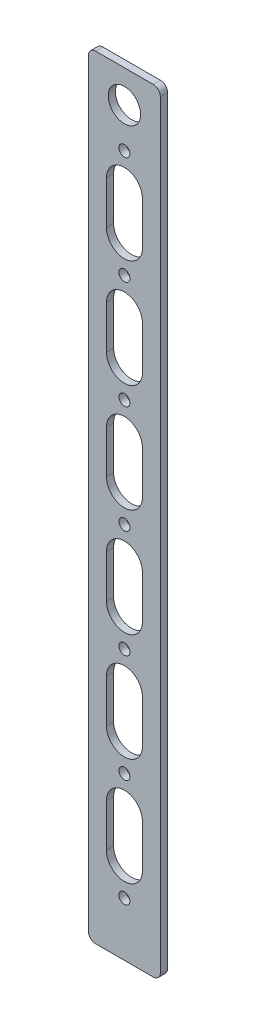
SolidWorks part; units mm, degrees
material "环氧玻璃布层压板"
ref_plane "前视基准面" through (0, 0, 0) normal (0, 0, 1) x (1, 0, 0)
ref_plane "上视基准面" through (0, 0, 0) normal (0, 1, 0) x (1, 0, 0)
ref_plane "右视基准面" through (0, 0, 0) normal (1, 0, 0) x (0, 0, -1)
sketch "草图1" plane through (0, 0, 0) normal (0, 0, 1) x (1, 0, 0)
  line L1 (-10, -107.5) -> (10, -107.5)
  line L2 (-10, -107.5) -> (-10, 107.5)
  line L3 (-10, 107.5) -> (10, 107.5)
  line L4 (10, -107.5) -> (10, 107.5)
  line L5 (0, 107.5) -> (0, -107.5) construction
  line L6 (-10, 0) -> (10, 0) construction
  point P0 (0, 0)
  dimension "D1" = 20
  dimension "D2" = 215
extrude "凸台-拉伸1" add sketch "草图1" along normal blind 2
fillet "圆角1" radius 2 4 edges at (10, -107.5, 1) (-10, -107.5, 1) (10, 107.5, 1) (-10, 107.5, 1)
sketch "草图2" plane through (0, 0, 2) normal (0, 0, 1) x (1, 0, 0)
  circle A0 centre (0, 87.5) radius 1.525 construction
  circle A1 centre (0, 57.5) radius 1.525 construction
  circle A2 centre (0, 27.5) radius 1.525 construction
  circle A3 centre (0, -2.5) radius 1.525 construction
  circle A4 centre (0, -32.5) radius 1.525 construction
  circle A5 centre (0, -62.5) radius 1.525 construction
  circle A6 centre (0, -92.5) radius 1.525 construction
  circle A7 centre (0, 87.5) radius 1.525
  circle A8 centre (0, 57.5) radius 1.525
  circle A9 centre (0, 27.5) radius 1.525
  circle A10 centre (0, -2.5) radius 1.525
  circle A11 centre (0, -32.5) radius 1.525
  circle A12 centre (0, -62.5) radius 1.525
  circle A13 centre (0, -92.5) radius 1.525
extrude "切除-拉伸1" cut sketch "草图2" against normal blind 10
sketch "草图4" plane through (0, 0, 2) normal (0, 0, 1) x (1, 0, 0)
  line L2 (5, 66.5) -> (5, 78.5)
  line L3 (-5, 78.5) -> (-5, 66.5)
  line L4 (5, 66.5) -> (5, 78.5)
  line L5 (-5, 78.5) -> (-5, 66.5)
  line L6 (5, 36.5) -> (5, 48.5)
  line L7 (-5, 48.5) -> (-5, 36.5)
  line L8 (5, 36.5) -> (5, 48.5)
  line L9 (-5, 48.5) -> (-5, 36.5)
  line L10 (5, -83.5) -> (5, -71.5)
  line L11 (-5, -71.5) -> (-5, -83.5)
  line L12 (5, -83.5) -> (5, -71.5)
  line L13 (-5, -71.5) -> (-5, -83.5)
  line L14 (5, 6.5) -> (5, 18.5)
  line L15 (-5, 18.5) -> (-5, 6.5)
  line L16 (5, 6.5) -> (5, 18.5)
  line L17 (-5, 18.5) -> (-5, 6.5)
  line L18 (5, -23.5) -> (5, -11.5)
  line L19 (-5, -11.5) -> (-5, -23.5)
  line L20 (5, -23.5) -> (5, -11.5)
  line L21 (-5, -11.5) -> (-5, -23.5)
  line L22 (5, -53.5) -> (5, -41.5)
  line L23 (-5, -41.5) -> (-5, -53.5)
  line L24 (5, -53.5) -> (5, -41.5)
  line L25 (-5, -41.5) -> (-5, -53.5)
  circle A1 centre (0, 98.5) radius 4.5
  circle A2 centre (0, 98.5) radius 4.5
  circle A3 centre (0, -103.5) radius 4.5
  arc A4 (-5, 66.5) -> (5, 66.5) centre (0, 66.5) ccw
  arc A5 (5, 78.5) -> (-5, 78.5) centre (0, 78.5) ccw
  arc A6 (-5, 66.5) -> (5, 66.5) centre (0, 66.5) ccw
  arc A7 (5, 78.5) -> (-5, 78.5) centre (0, 78.5) ccw
  arc A8 (5, 48.5) -> (-5, 48.5) centre (0, 48.5) ccw
  arc A9 (-5, 36.5) -> (5, 36.5) centre (0, 36.5) ccw
  arc A10 (5, 48.5) -> (-5, 48.5) centre (0, 48.5) ccw
  arc A11 (-5, 36.5) -> (5, 36.5) centre (0, 36.5) ccw
  arc A12 (5, -71.5) -> (-5, -71.5) centre (0, -71.5) ccw
  arc A13 (-5, -83.5) -> (5, -83.5) centre (0, -83.5) ccw
  arc A14 (5, -71.5) -> (-5, -71.5) centre (0, -71.5) ccw
  arc A15 (-5, -83.5) -> (5, -83.5) centre (0, -83.5) ccw
  arc A16 (-5, 6.5) -> (5, 6.5) centre (0, 6.5) ccw
  arc A17 (5, 18.5) -> (-5, 18.5) centre (0, 18.5) ccw
  arc A18 (-5, 6.5) -> (5, 6.5) centre (0, 6.5) ccw
  arc A19 (5, 18.5) -> (-5, 18.5) centre (0, 18.5) ccw
  arc A20 (5, -11.5) -> (-5, -11.5) centre (0, -11.5) ccw
  arc A21 (-5, -23.5) -> (5, -23.5) centre (0, -23.5) ccw
  arc A22 (5, -11.5) -> (-5, -11.5) centre (0, -11.5) ccw
  arc A23 (-5, -23.5) -> (5, -23.5) centre (0, -23.5) ccw
  arc A24 (-5, -53.5) -> (5, -53.5) centre (0, -53.5) ccw
  arc A25 (5, -41.5) -> (-5, -41.5) centre (0, -41.5) ccw
  arc A26 (-5, -53.5) -> (5, -53.5) centre (0, -53.5) ccw
  arc A27 (5, -41.5) -> (-5, -41.5) centre (0, -41.5) ccw
  circle A28 centre (0, -103.5) radius 4.5 construction
  dimension "D1" = 0
  dimension "D2" = 0
  dimension "D3" = 0
  dimension "D4" = 0
  dimension "D5" = 0
  dimension "D6" = 0
  dimension "D7" = 0
  dimension "D8" = 0
extrude "切除-拉伸2" cut sketch "草图4" against normal blind 10
